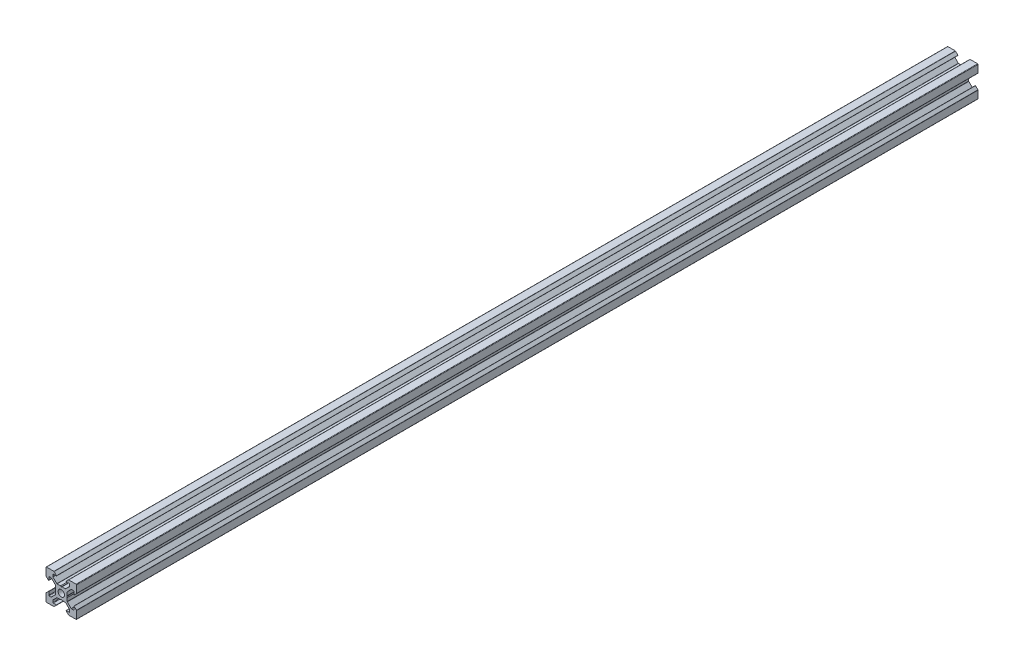
SolidWorks part; units mm, degrees
material "6063-T5"
ref_plane "Plan de face" through (0, 0, 0) normal (0, 0, 1) x (1, 0, 0)
ref_plane "Plan de dessus" through (0, 0, 0) normal (0, 1, 0) x (1, 0, 0)
ref_plane "Plan de droite" through (0, 0, 0) normal (1, 0, 0) x (0, 0, -1)
sketch "Esquisse1" plane through (0, 0, 0) normal (0, 0, 1) x (1, 0, 0)
  line L0 (18.7749, -2.8952) -> (18.7749, -4.8946)
  line L1 (18.4749, -5.1946) -> (17.2591, -5.1946)
  line L2 (17.047, -5.1067) -> (14.5634, -2.6231)
  line L3 (14.4755, -2.411) -> (14.4755, -0.2148)
  line L4 (14.4755, -0.2148) -> (14.1755, 0.3048)
  line L5 (14.1755, 0.3048) -> (14.4755, 0.8244)
  line L6 (14.4755, 0.8244) -> (14.4755, 3.0205)
  line L7 (14.5634, 3.2326) -> (17.047, 5.7162)
  line L8 (17.2591, 5.8041) -> (18.4749, 5.8041)
  line L9 (18.7749, 5.5041) -> (18.7749, 3.5048)
  line L10 (18.9456, 3.4341) -> (20.487, 4.9755)
  line L11 (20.5749, 5.1876) -> (20.5749, 10.0048)
  line L12 (20.2749, 10.3048) -> (15.4577, 10.3048)
  line L13 (15.2456, 10.2169) -> (13.7041, 8.6755)
  line L14 (13.7749, 8.5048) -> (15.7742, 8.5048)
  line L15 (16.0742, 8.2048) -> (16.0742, 6.989)
  line L16 (15.9863, 6.7769) -> (13.5027, 4.2933)
  line L17 (13.2906, 4.2054) -> (11.0945, 4.2054)
  line L18 (11.0945, 4.2054) -> (10.5749, 3.9054)
  line L19 (10.5749, 3.9054) -> (10.0552, 4.2054)
  line L20 (10.0552, 4.2054) -> (7.8591, 4.2054)
  line L21 (7.647, 4.2933) -> (5.1634, 6.7769)
  line L22 (5.0755, 6.989) -> (5.0755, 8.2048)
  line L23 (5.3755, 8.5048) -> (7.3749, 8.5048)
  line L24 (7.4456, 8.6755) -> (5.9041, 10.2169)
  line L25 (5.692, 10.3048) -> (0.8749, 10.3048)
  line L26 (0.5749, 10.0048) -> (0.5749, 5.1876)
  line L27 (0.6627, 4.9755) -> (2.2041, 3.4341)
  line L28 (2.3749, 3.5048) -> (2.3749, 5.5041)
  line L29 (2.6749, 5.8041) -> (3.8906, 5.8041)
  line L30 (4.1027, 5.7162) -> (6.5863, 3.2326)
  line L31 (6.6742, 3.0205) -> (6.6742, 0.8244)
  line L32 (6.6742, 0.8244) -> (6.9742, 0.3048)
  line L33 (6.9742, 0.3048) -> (6.6742, -0.2148)
  line L34 (6.6742, -0.2148) -> (6.6742, -2.411)
  line L35 (6.5863, -2.6231) -> (4.1027, -5.1067)
  line L36 (3.8906, -5.1946) -> (2.6749, -5.1946)
  line L37 (2.3749, -4.8946) -> (2.3749, -2.8952)
  line L38 (2.2041, -2.8245) -> (0.6627, -4.3659)
  line L39 (0.5749, -4.5781) -> (0.5749, -9.3952)
  line L40 (0.8749, -9.6952) -> (5.692, -9.6952)
  line L41 (5.9041, -9.6074) -> (7.4456, -8.0659)
  line L42 (7.3749, -7.8952) -> (5.3755, -7.8952)
  line L43 (5.0755, -7.5952) -> (5.0755, -6.3795)
  line L44 (5.1634, -6.1674) -> (7.647, -3.6838)
  line L45 (7.8591, -3.5959) -> (10.0552, -3.5959)
  line L46 (10.0552, -3.5959) -> (10.5749, -3.2959)
  line L47 (10.5749, -3.2959) -> (11.0945, -3.5959)
  line L48 (11.0945, -3.5959) -> (13.2906, -3.5959)
  line L49 (13.5027, -3.6838) -> (15.9863, -6.1674)
  line L50 (16.0742, -6.3795) -> (16.0742, -7.5952)
  line L51 (15.7742, -7.8952) -> (13.7749, -7.8952)
  line L52 (13.7041, -8.0659) -> (15.2456, -9.6074)
  line L53 (15.4577, -9.6952) -> (20.2749, -9.6952)
  line L54 (20.5749, -9.3952) -> (20.5749, -4.5781)
  line L55 (20.487, -4.3659) -> (18.9456, -2.8245)
  arc A0 (10.5749, -1.7952) -> (12.6749, 0.3048) centre (10.5749, 0.3048) ccw
  arc A1 (12.6749, 0.3048) -> (10.5749, 2.4048) centre (10.5749, 0.3048) ccw
  arc A2 (10.5749, 2.4048) -> (8.4749, 0.3048) centre (10.5749, 0.3048) ccw
  arc A3 (8.4749, 0.3048) -> (10.5749, -1.7952) centre (10.5749, 0.3048) ccw
  arc A4 (18.9456, -2.8245) -> (18.7749, -2.8952) centre (18.8749, -2.8952) ccw
  arc A5 (18.4749, -5.1946) -> (18.7749, -4.8946) centre (18.4749, -4.8946) ccw
  arc A6 (17.047, -5.1067) -> (17.2591, -5.1946) centre (17.2591, -4.8946) ccw
  arc A7 (14.4755, -2.411) -> (14.5634, -2.6231) centre (14.7755, -2.411) ccw
  arc A8 (14.5634, 3.2326) -> (14.4755, 3.0205) centre (14.7755, 3.0205) ccw
  arc A9 (17.2591, 5.8041) -> (17.047, 5.7162) centre (17.2591, 5.5041) ccw
  arc A10 (18.7749, 5.5041) -> (18.4749, 5.8041) centre (18.4749, 5.5041) ccw
  arc A11 (18.7749, 3.5048) -> (18.9456, 3.4341) centre (18.8749, 3.5048) ccw
  arc A12 (20.487, 4.9755) -> (20.5749, 5.1876) centre (20.2749, 5.1876) ccw
  arc A13 (20.5749, 10.0048) -> (20.2749, 10.3048) centre (20.2749, 10.0048) ccw
  arc A14 (15.4577, 10.3048) -> (15.2456, 10.2169) centre (15.4577, 10.0048) ccw
  arc A15 (13.7041, 8.6755) -> (13.7749, 8.5048) centre (13.7749, 8.6048) ccw
  arc A16 (16.0742, 8.2048) -> (15.7742, 8.5048) centre (15.7742, 8.2048) ccw
  arc A17 (15.9863, 6.7769) -> (16.0742, 6.989) centre (15.7742, 6.989) ccw
  arc A18 (13.2906, 4.2054) -> (13.5027, 4.2933) centre (13.2906, 4.5054) ccw
  arc A19 (7.647, 4.2933) -> (7.8591, 4.2054) centre (7.8591, 4.5054) ccw
  arc A20 (5.0755, 6.989) -> (5.1634, 6.7769) centre (5.3755, 6.989) ccw
  arc A21 (5.3755, 8.5048) -> (5.0755, 8.2048) centre (5.3755, 8.2048) ccw
  arc A22 (7.3749, 8.5048) -> (7.4456, 8.6755) centre (7.3749, 8.6048) ccw
  arc A23 (5.9041, 10.2169) -> (5.692, 10.3048) centre (5.692, 10.0048) ccw
  arc A24 (0.8749, 10.3048) -> (0.5749, 10.0048) centre (0.8749, 10.0048) ccw
  arc A25 (0.5749, 5.1876) -> (0.6627, 4.9755) centre (0.8749, 5.1876) ccw
  arc A26 (2.2041, 3.4341) -> (2.3749, 3.5048) centre (2.2749, 3.5048) ccw
  arc A27 (2.6749, 5.8041) -> (2.3749, 5.5041) centre (2.6749, 5.5041) ccw
  arc A28 (4.1027, 5.7162) -> (3.8906, 5.8041) centre (3.8906, 5.5041) ccw
  arc A29 (6.6742, 3.0205) -> (6.5863, 3.2326) centre (6.3742, 3.0205) ccw
  arc A30 (6.5863, -2.6231) -> (6.6742, -2.411) centre (6.3742, -2.411) ccw
  arc A31 (3.8906, -5.1946) -> (4.1027, -5.1067) centre (3.8906, -4.8946) ccw
  arc A32 (2.3749, -4.8946) -> (2.6749, -5.1946) centre (2.6749, -4.8946) ccw
  arc A33 (2.3749, -2.8952) -> (2.2041, -2.8245) centre (2.2749, -2.8952) ccw
  arc A34 (0.6627, -4.3659) -> (0.5749, -4.5781) centre (0.8749, -4.5781) ccw
  arc A35 (0.5749, -9.3952) -> (0.8749, -9.6952) centre (0.8749, -9.3952) ccw
  arc A36 (5.692, -9.6952) -> (5.9041, -9.6074) centre (5.692, -9.3952) ccw
  arc A37 (7.4456, -8.0659) -> (7.3749, -7.8952) centre (7.3749, -7.9952) ccw
  arc A38 (5.0755, -7.5952) -> (5.3755, -7.8952) centre (5.3755, -7.5952) ccw
  arc A39 (5.1634, -6.1674) -> (5.0755, -6.3795) centre (5.3755, -6.3795) ccw
  arc A40 (7.8591, -3.5959) -> (7.647, -3.6838) centre (7.8591, -3.8959) ccw
  arc A41 (13.5027, -3.6838) -> (13.2906, -3.5959) centre (13.2906, -3.8959) ccw
  arc A42 (16.0742, -6.3795) -> (15.9863, -6.1674) centre (15.7742, -6.3795) ccw
  arc A43 (15.7742, -7.8952) -> (16.0742, -7.5952) centre (15.7742, -7.5952) ccw
  arc A44 (13.7749, -7.8952) -> (13.7041, -8.0659) centre (13.7749, -7.9952) ccw
  arc A45 (15.2456, -9.6074) -> (15.4577, -9.6952) centre (15.4577, -9.3952) ccw
  arc A46 (20.2749, -9.6952) -> (20.5749, -9.3952) centre (20.2749, -9.3952) ccw
  arc A47 (20.5749, -4.5781) -> (20.487, -4.3659) centre (20.2749, -4.5781) ccw
extrude "Boss.-Extru.1" add sketch "Esquisse1" along normal blind 590
